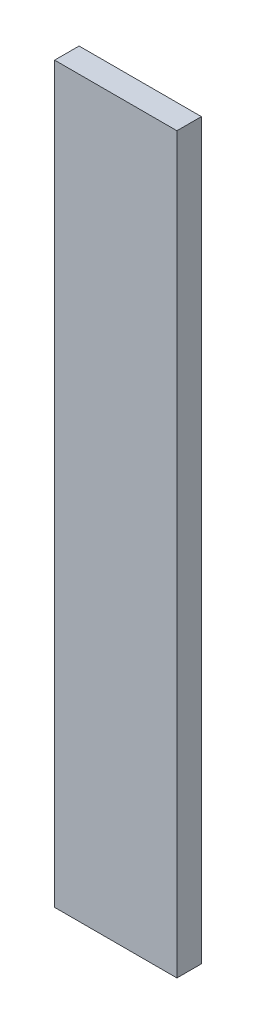
SolidWorks part; units mm, degrees
ref_plane "Plan de face" through (0, 0, 0) normal (0, 0, 1) x (1, 0, 0)
ref_plane "Plan de dessus" through (0, 0, 0) normal (0, 1, 0) x (1, 0, 0)
ref_plane "Plan de droite" through (0, 0, 0) normal (1, 0, 0) x (0, 0, -1)
sketch "Esquisse1" plane through (0, 0, 0) normal (0, 0, 1) x (1, 0, 0)
  line L0 (0, 0) -> (0, 300)
  line L1 (0, 300) -> (50, 300)
  line L2 (50, 300) -> (50, 0)
  line L3 (50, 0) -> (0, 0)
  dimension "D1" = 300
  dimension "D2" = 50
extrude "Boss.-Extru.1" add sketch "Esquisse1" along normal blind 10 contours L2 L3 L0 L1
